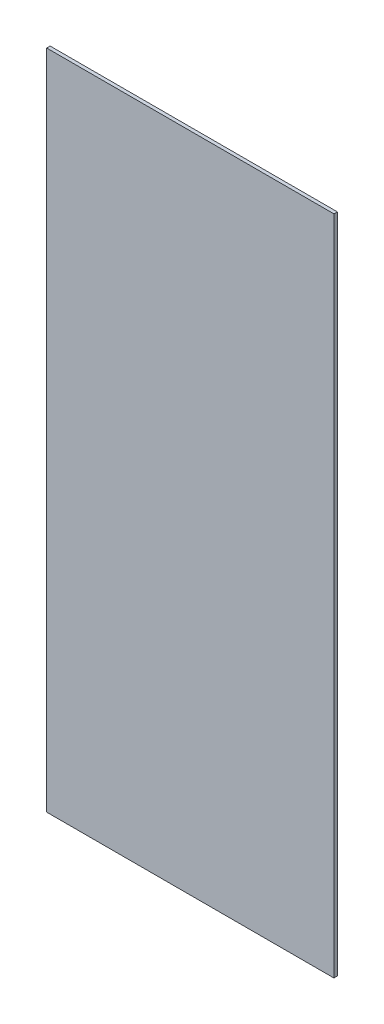
SolidWorks part; units mm, degrees
ref_plane "Front Plane" through (0, 0, 0) normal (0, 0, 1) x (1, 0, 0)
ref_plane "Top Plane" through (0, 0, 0) normal (0, 1, 0) x (1, 0, 0)
ref_plane "Right Plane" through (0, 0, 0) normal (1, 0, 0) x (0, 0, -1)
sketch "Sketch1" plane through (0, 0, 0) normal (0, 0, 1) x (1, 0, 0)
  line L1 (-125, -288) -> (125, -288)
  line L2 (-125, -288) -> (-125, 288)
  line L3 (-125, 288) -> (125, 288)
  line L4 (125, -288) -> (125, 288)
  line L5 (-125, -288) -> (125, 288) construction
  line L6 (-125, 288) -> (125, -288) construction
  point P0 (0, 0)
  dimension "D1" = 250
  dimension "D2" = 576
extrude "Boss-Extrude1" add sketch "Sketch1" along normal blind 3
